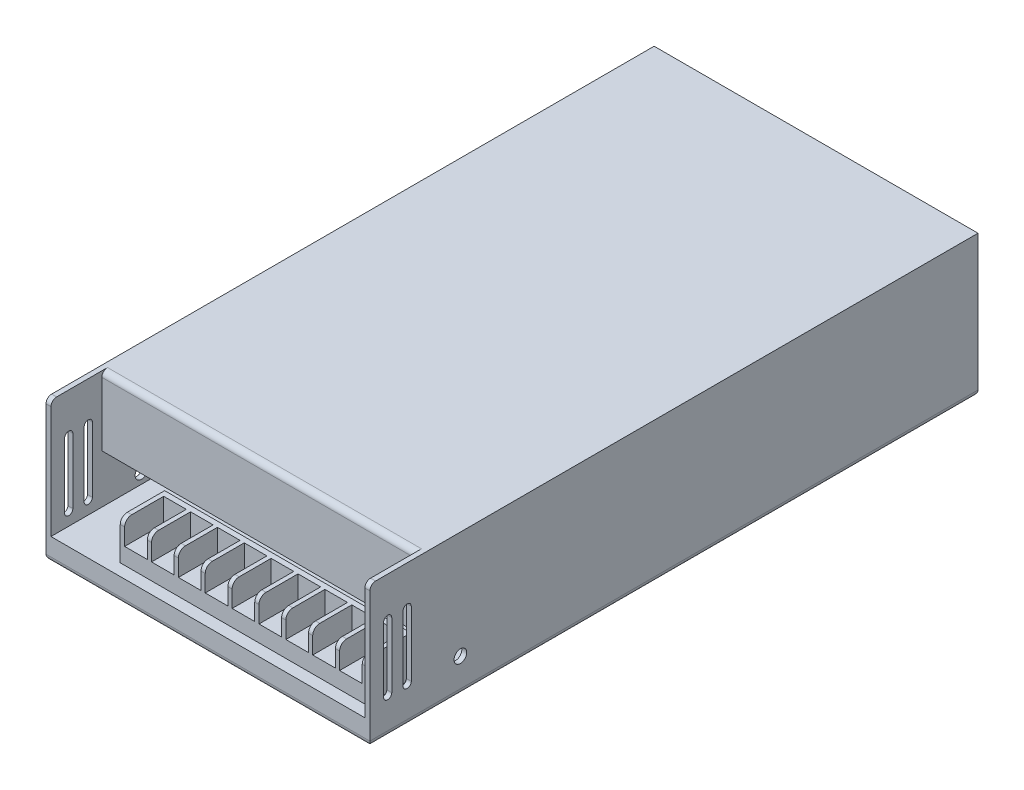
SolidWorks part; units mm, degrees
material "2024 Alloy"
ref_plane "Front Plane" through (0, 0, 0) normal (0, 0, 1) x (1, 0, 0)
ref_plane "Top Plane" through (0, 0, 0) normal (0, 1, 0) x (1, 0, 0)
ref_plane "Right Plane" through (0, 0, 0) normal (1, 0, 0) x (0, 0, -1)
sketch "Sketch1" plane through (0, 0, 0) normal (0, 1, 0) x (1, 0, 0)
  line L0 (0, 197) -> (0, -18) construction
  line L1 (-57.25, -18) -> (57.25, -18)
  line L2 (-57.25, -18) -> (-57.25, 197)
  line L3 (-57.25, 197) -> (57.25, 197)
  line L4 (57.25, -18) -> (57.25, 197)
  line L5 (-57.25, 0) -> (57.25, 0) construction
  dimension "D1" = 215
  dimension "D2" = 18
  dimension "D3" = 114.5
extrude "Boss-Extrude1" add sketch "Sketch1" along normal blind 41.75 and the other way blind 8.25
sketch "Sketch2" plane through (0, 0, 18) normal (0, 0, 1) x (1, 0, 0)
  line L0 (-57.25, 41.75) -> (57.25, 41.75) construction
  line L1 (-55.5, 0) -> (55.5, 0)
  line L2 (-55.5, 0) -> (-55.5, 41.75)
  line L3 (-55.5, 41.75) -> (55.5, 41.75)
  line L4 (55.5, 0) -> (55.5, 41.75)
  line L5 (0, 0) -> (0, 41.75) construction
  line L6 (57.25, -8.25) -> (57.25, 41.75) construction
  dimension "D1" = 1.75
extrude "Cut-Extrude1" cut sketch "Sketch2" against normal blind 18
sketch "Sketch3" plane through (57.25, 0, 0) normal (1, 0, 0) x (0, 0, -1)
  line L0 (-11.71, 27.7) -> (-11.71, 4.7) construction
  line L1 (-10.26, 27.7) -> (-10.26, 4.7)
  line L2 (-13.16, 27.7) -> (-13.16, 4.7)
  line L3 (-4.81, 27.7) -> (-4.81, 4.7) construction
  line L4 (-3.36, 27.7) -> (-3.36, 4.7)
  line L5 (-6.26, 27.7) -> (-6.26, 4.7)
  line L6 (-11.71, 16.2) -> (-4.81, 16.2) construction
  line L7 (-18, -8.25) -> (-18, 41.75) construction
  line L8 (-11.71, 29.15) -> (-11.71, 41.75) construction
  line L9 (-18, 41.75) -> (197, 41.75) construction
  line L10 (-11.71, 3.25) -> (-11.71, -8.25) construction
  line L11 (-18, -8.25) -> (197, -8.25) construction
  arc A0 (-10.26, 27.7) -> (-13.16, 27.7) centre (-11.71, 27.7) ccw
  arc A1 (-13.16, 4.7) -> (-10.26, 4.7) centre (-11.71, 4.7) ccw
  arc A2 (-3.36, 27.7) -> (-6.26, 27.7) centre (-4.81, 27.7) ccw
  arc A3 (-6.26, 4.7) -> (-3.36, 4.7) centre (-4.81, 4.7) ccw
  point P2 (-11.71, 16.2)
  point P7 (-4.81, 16.2)
  dimension "D1" = 4.84
  dimension "D2" = 2.9
  dimension "D3" = 4
  dimension "D4" = 12.6
  dimension "D5" = 11.5
extrude "Cut-Extrude2" cut sketch "Sketch3" against normal through all
fillet "Fillet1" radius 2 7 edges at (0, -8.25, -197) (-57.25, -8.25, -89.5) (0, -8.25, 18) (57.25, -8.25, -89.5) (0, 41.75, 0) (56.375, 41.75, 18) (-56.375, 41.75, 18)
sketch "Sketch4" plane through (0, 0, 0) normal (0, 1, 0) x (-1, 0, 0)
  line L0 (55.5, 0) -> (-55.5, 0) construction
  line L1 (35.2, 0) -> (-51.85, 0)
  line L2 (35.2, 0) -> (35.2, 13.8)
  line L3 (35.2, 13.8) -> (-51.85, 13.8)
  line L4 (-51.85, 0) -> (-51.85, 13.8)
  line L5 (55.5, 18) -> (-55.5, 18) construction
  line L6 (-55.5, 0) -> (-55.5, 18) construction
  line L7 (55.5, 0) -> (55.5, 18) construction
  dimension "D1" = 4.2
  dimension "D2" = 3.65
  dimension "D3" = 20.3
extrude "Boss-Extrude2" add sketch "Sketch4" along normal blind 14.25 separate body
sketch "Sketch7" plane through (0, 0, 0) normal (0, 0, 1) x (1, 0, 0)
  line L0 (-55.5, 39.75) -> (-55.5, 0) construction
  line L1 (-55.5, 17.25) -> (55.5, 17.25)
  line L2 (-55.5, 17.25) -> (-55.5, 0)
  line L3 (-55.5, 0) -> (55.5, 0)
  line L4 (55.5, 17.25) -> (55.5, 0)
  line L5 (-55.5, 0) -> (55.5, 0) construction
  line L6 (51.85, 14.25) -> (-35.2, 14.25) construction
  line L7 (55.5, 0) -> (55.5, 39.75) construction
  dimension "D1" = 3
extrude "Cut-Extrude4" cut sketch "Sketch7" against normal offset from surface (195.25 mm away) 1.75 up to face at (0, 17.75, -197)
fillet "Fillet2" radius 2.5 1 edges at (8.325, 14.25, 13.8)
sketch "Sketch6" plane through (0, 0, 13.8) normal (0, 0, 1) x (1, 0, 0)
  line L0 (-35.2, 14.25) -> (51.85, 14.25) construction
  line L1 (42.35, 14.25) -> (50.35, 14.25)
  line L2 (42.35, 14.25) -> (42.35, 5.8)
  line L3 (42.35, 5.8) -> (50.35, 5.8)
  line L4 (50.35, 14.25) -> (50.35, 5.8)
  line L6 (51.85, 11.75) -> (51.85, 0) construction
  line L7 (-35.2, 0) -> (51.85, 0) construction
  dimension "D1" = 5.8
  dimension "D2" = 1.5
  dimension "D3" = 8
extrude "Cut-Extrude3" cut sketch "Sketch6" against normal up to surface (13.8 mm away) up to face at (0, 28.5, 0)
sketch "Sketch9" plane through (0, 0, 0) normal (0, 0, -1) x (-1, 0, 0)
  line L0 (35.2, 14.25) -> (35.2, 0) construction
  line L1 (-51.85, 14.25) -> (35.2, 14.25)
  line L2 (-51.85, 14.25) -> (-51.85, 0.5)
  line L3 (-51.85, 0.5) -> (35.2, 0.5)
  line L4 (35.2, 14.25) -> (35.2, 0.5)
  line L5 (-51.85, 0) -> (35.2, 0) construction
  dimension "D1" = 0.5
extrude "Boss-Extrude6" add sketch "Sketch9" along normal blind 1.9
pattern_linear "LPattern1" count 9 spacing 9.5 along (-1, 0, 0) of "Cut-Extrude3"
hole_wizard "M3 Clearance Hole2" positions "Sketch14" profile "Sketch13" hole size "M3" standard "Ansi Metric"
sketch "Sketch14" plane through (0, -8.25, 0) normal (0, -1, 0) x (1, 0, 0)
  line L0 (-57.25, 18) -> (57.25, 18) construction
  line L2 (-57.25, -197) -> (-57.25, 18) construction
  line L3 (57.25, -197) -> (-57.25, -197) construction
  line L4 (57.25, 18) -> (57.25, -197) construction
  point P0 (-47.5, -8.75)
  point P1 (47.5, -8.75)
  point P3 (47.5, -186.5)
  point P5 (-47.5, -186.5)
  dimension "D1" = 26.75
  dimension "D2" = 9.75
  dimension "D3" = 10.5
  dimension "D4" = 9.75
sketch "Sketch13" plane through (-47.5, -8.25, -8.75) normal (1, 0, 0) x (0, 0, -1)
  line L0 (0, 0) -> (0, 3.0215)
  line L1 (0, 3.0215) -> (1.7, 2)
  line L2 (1.7, 2) -> (1.7, 0)
  line L5 (1.7, 0) -> (0, 0)
  line L10 (0, 3.0215) -> (-1.7, 2) construction
  line L11 (0, -6.35) -> (0, 107.95) construction
  dimension "Hole Dia." = 3.4
  dimension "Hole Depth" = 2
  dimension "Drill Angle" = 118
hole_wizard "M4 Clearance Hole1" positions "Sketch16" profile "Sketch15" hole size "M4" standard "Ansi Metric"
sketch "Sketch16" plane through (57.25, 0, 0) normal (1, 0, 0) x (0, 0, -1)
  line L0 (-18, -6.25) -> (-18, 39.75) construction
  line L1 (195, -8.25) -> (-16, -8.25) construction
  point P0 (14, 3.75)
  dimension "D1" = 32
  dimension "D2" = 12
sketch "Sketch15" plane through (57.25, 3.75, -14) normal (0, 1, 0) x (0, 0, -1)
  line L0 (0, 0) -> (0, 3.3519)
  line L1 (0, 3.3519) -> (2.25, 2)
  line L2 (2.25, 2) -> (2.25, 0)
  line L5 (2.25, 0) -> (0, 0)
  line L10 (0, 3.3519) -> (-2.25, 2) construction
  line L11 (0, -6.35) -> (0, 107.95) construction
  dimension "Hole Dia." = 4.5
  dimension "Hole Depth" = 2
  dimension "Drill Angle" = 118
mirror "M4 Hole Other Side" about plane through (0, 0, 0) normal (1, 0, 0) of "M4 Clearance Hole1"
